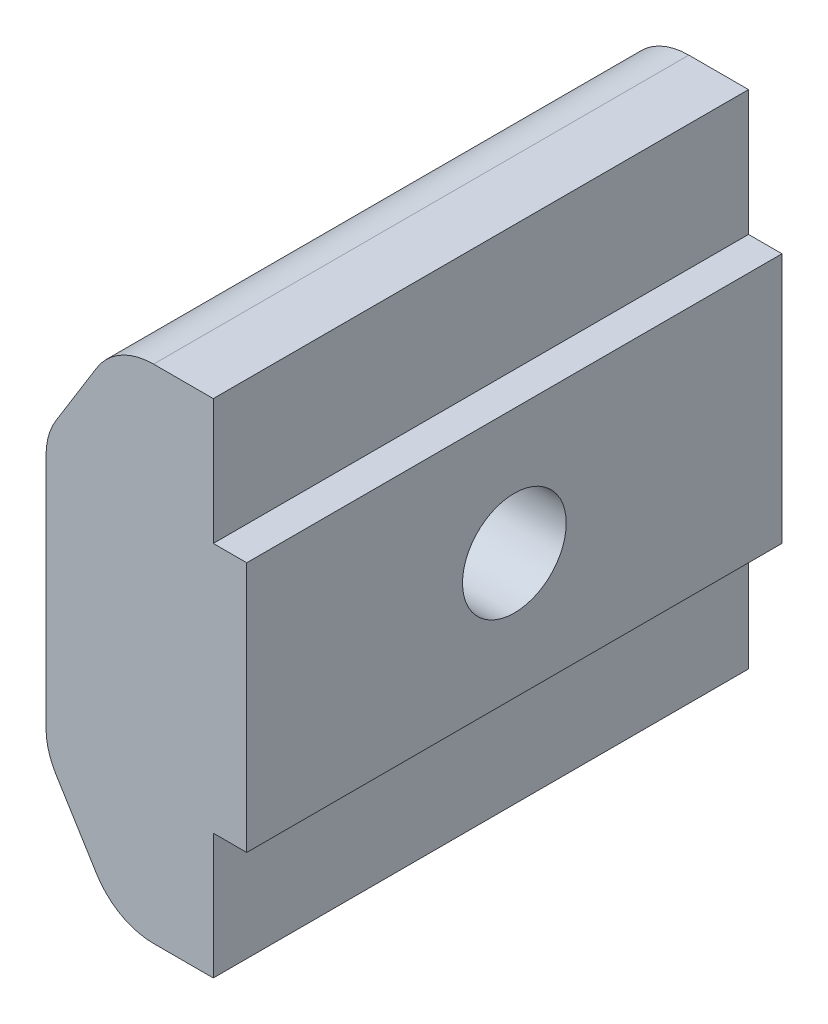
SolidWorks part; units mm, degrees
ref_plane "Alzado" through (0, 0, 0) normal (0, 0, 1) x (1, 0, 0)
ref_plane "Planta" through (0, 0, 0) normal (0, 1, 0) x (1, 0, 0)
ref_plane "Vista lateral" through (0, 0, 0) normal (1, 0, 0) x (0, 0, -1)
sketch "Croquis1" plane through (0, 0, 0) normal (0, 0, 1) x (1, 0, 0)
  line L0 (0, 12.5319) -> (0, 8.2) construction
  line L1 (2.1, -3.4) -> (5, -3.4)
  line L2 (0, 0) -> (0, 8.2)
  line L3 (2.1, 11.6) -> (5, 11.6)
  line L4 (5, -3.4) -> (5, 11.6)
  line L5 (5, 11.6) -> (2.1, 11.6) construction
  line L6 (0, 8.2) -> (2.1, 11.6)
  line L7 (5, 4.1) -> (0, 4.1) construction
  line L8 (0, 0) -> (2.1, -3.4)
  dimension "D1" = 5
  dimension "D2" = 15
  dimension "D3" = 3.4
  dimension "D4" = 2.9
extrude "Saliente-Extruir1" add sketch "Croquis1" along normal blind 16
sketch "Croquis2" plane through (0, 0, 0) normal (-1, 0, 0) x (0, 0, 1)
  line L0 (0, 4.1) -> (16, 4.1) construction
  line L1 (0, 8.2) -> (0, 0) construction
  line L2 (16, 8.2) -> (16, 0) construction
  line L3 (8, 8.2) -> (8, 0) construction
  line L4 (16, 8.2) -> (0, 8.2) construction
  line L5 (16, 0) -> (0, 0) construction
  circle A0 centre (8, 4.1) radius 1.55
  dimension "D1" = 3.1
extrude "Cortar-Extruir1" cut sketch "Croquis2" against normal up to surface (5 mm away) up to face at (5, 4.1, 8)
sketch "Croquis3" plane through (0, 0, 0) normal (-1, 0, 0) x (0, 0, 1)
  line L0 (0, 4.1) -> (16, 4.1) construction
  line L1 (11.3486, 4.1) -> (9.6743, 7)
  line L2 (9.6743, 7) -> (6.3257, 7)
  line L3 (6.3257, 7) -> (4.6514, 4.1)
  line L4 (4.6514, 4.1) -> (6.3257, 1.2)
  line L5 (6.3257, 1.2) -> (9.6743, 1.2)
  line L6 (9.6743, 1.2) -> (11.3486, 4.1)
  line L7 (0, 8.2) -> (0, 0) construction
  line L8 (16, 8.2) -> (16, 0) construction
  circle A0 centre (8, 4.1) radius 2.9 construction
  dimension "D1" = 5.8
extrude "Cortar-Extruir2" cut sketch "Croquis3" against normal blind 2.5
fillet "Redondeo1" radius 2 4 edges at (2.1, -3.4, 8) (0, 0, 8) (0, 8.2, 8) (2.1, 11.6, 8)
sketch "Croquis4" plane through (5, 0, 0) normal (1, 0, 0) x (0, 0, -1)
  line L0 (-16, 7.85) -> (0, 7.85)
  line L4 (-16, 7.85) -> (-16, 0.35)
  line L5 (0, -3.4) -> (0, 11.6) construction
  line L6 (-16, 0.35) -> (0, 0.35)
  line L7 (-16, -3.4) -> (-16, 11.6) construction
  line L8 (0, 7.85) -> (0, 0.35)
  line L9 (-16, -3.4) -> (0, -3.4) construction
  circle A0 centre (-8, 4.1) radius 1.55 construction
  circle A1 centre (-8, 4.1) radius 1.55
  dimension "D1" = 7.5
  dimension "D2" = 3.75
extrude "Saliente-Extruir3" add sketch "Croquis4" along normal blind 1
